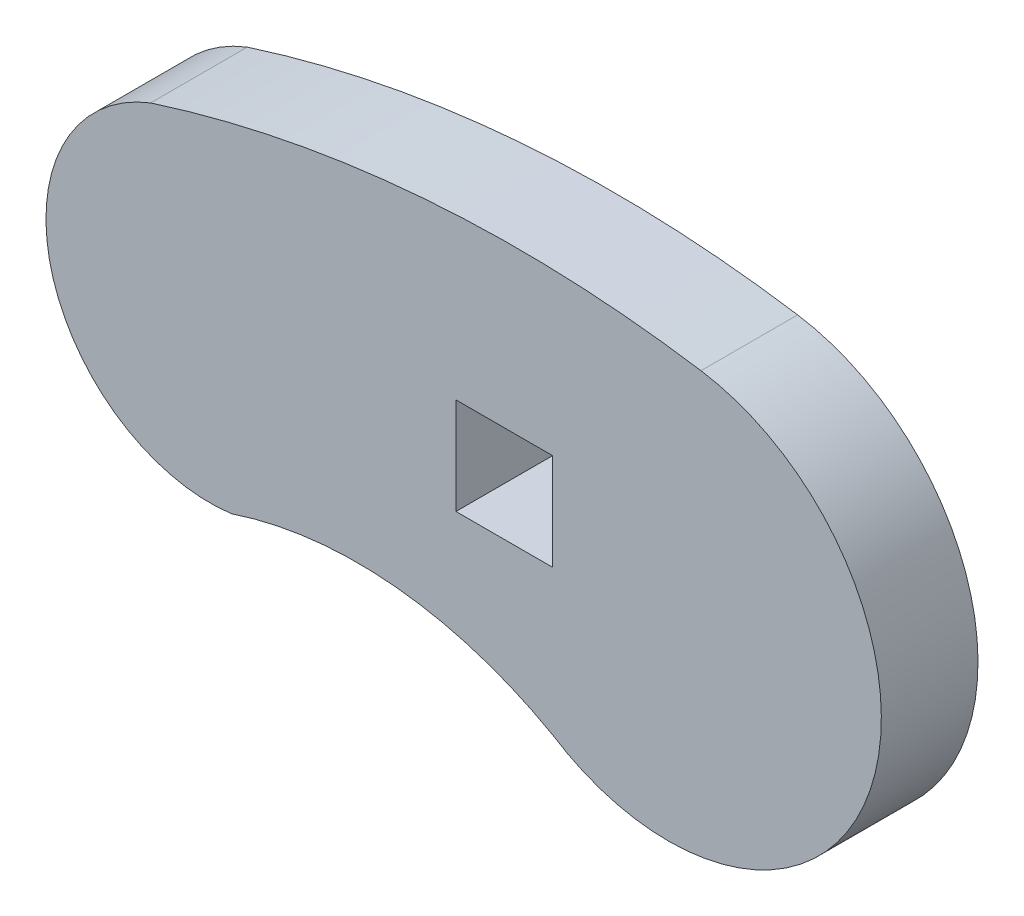
SolidWorks part; units mm, degrees
ref_plane "Front Plane" through (0, 0, 0) normal (0, 0, 1) x (1, 0, 0)
ref_plane "Top Plane" through (0, 0, 0) normal (0, 1, 0) x (1, 0, 0)
ref_plane "Right Plane" through (0, 0, 0) normal (1, 0, 0) x (0, 0, -1)
sketch "Sketch1" plane through (0, 0, 0) normal (0, 0, 1) x (1, 0, 0)
  line L0 (1.524, -2.0168) -> (1.524, -4.5416) construction
  line L1 (0, 0) -> (1.524, 0)
  line L2 (1.524, 0) -> (1.524, -1.524)
  line L3 (1.524, -1.524) -> (0, -1.524)
  line L4 (0, -1.524) -> (0, 0)
  arc A0 (-4.813, 1.6474) -> (-3.5358, -3.3235) centre (-3.8784, -0.762) ccw
  arc A1 (1.524, -3.8116) -> (3.8633, 2.3298) centre (3.3469, -0.9897) ccw
  arc A2 (-3.5358, -3.3235) -> (1.524, -3.8116) centre (-1.5527, -9.2355) cw
  arc A3 (-4.813, 1.6474) -> (3.8633, 2.3298) centre (0.9642, -16.3085) cw
extrude "Boss-Extrude1" add sketch "Sketch1" along normal blind 1.524
